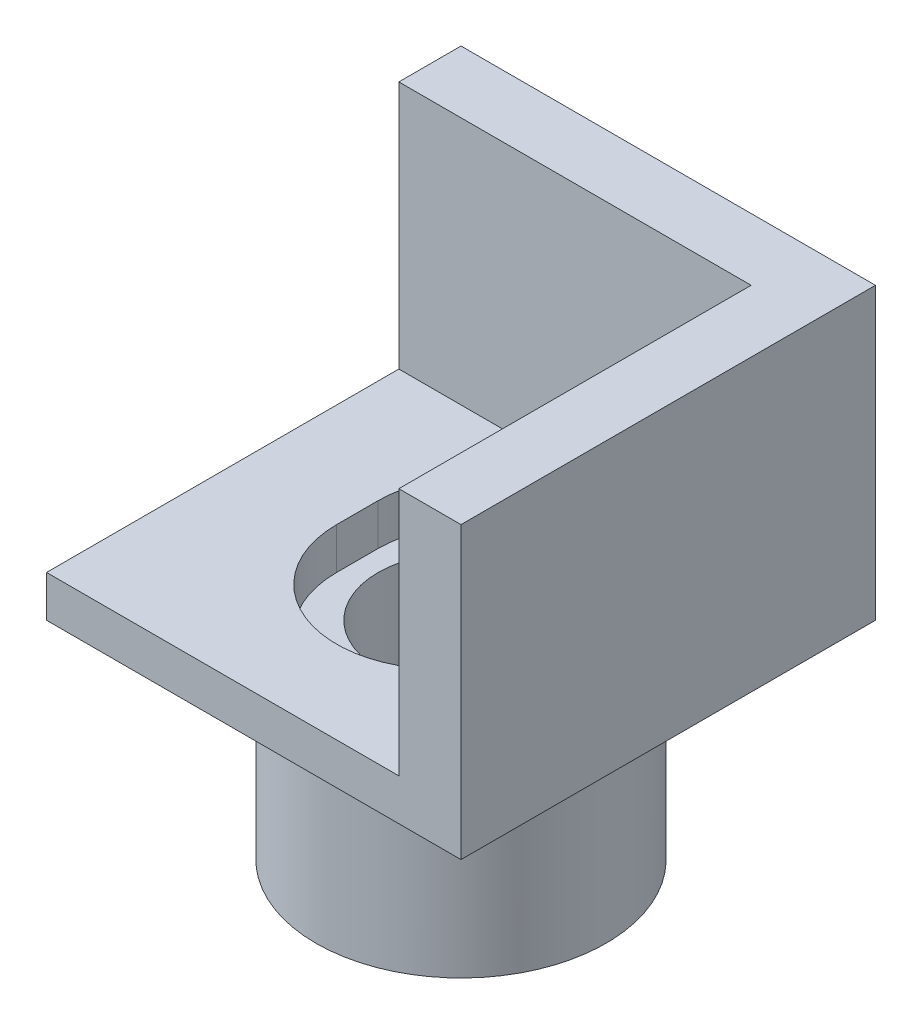
SolidWorks part; units mm, degrees
ref_plane "Front Plane" through (0, 0, 0) normal (0, 0, 1) x (1, 0, 0)
ref_plane "Top Plane" through (0, 0, 0) normal (0, 1, 0) x (1, 0, 0)
ref_plane "Right Plane" through (0, 0, 0) normal (1, 0, 0) x (0, 0, -1)
sketch "Sketch1" plane through (0, 0, 0) normal (0, 1, 0) x (1, 0, 0)
  line L0 (5, 5) -> (-5, -5) construction
  line L1 (-5, 5) -> (5, 5)
  line L2 (-5, 5) -> (-5, -5)
  line L3 (-5, -5) -> (5, -5)
  line L4 (5, 5) -> (5, -5)
  line L5 (5, -5) -> (-5, 5) construction
  point P0 (0, 0)
  dimension "D1" = 10
  dimension "D2" = 10
extrude "Boss-Extrude1" add sketch "Sketch1" along normal blind 1
sketch "Sketch2" plane through (0, 1, 0) normal (0, 1, 0) x (1, 0, 0)
  line L0 (0, 0.5) -> (0, -0.5) construction
  line L1 (2.5, 0.5) -> (2.5, -0.5)
  line L2 (-2.5, 0.5) -> (-2.5, -0.5)
  arc A0 (2.5, 0.5) -> (-2.5, 0.5) centre (0, 0.5) ccw
  arc A1 (-2.5, -0.5) -> (2.5, -0.5) centre (0, -0.5) ccw
  point P2 (0, 0)
  point P7 (0, 3)
  point P8 (0, -3)
  point P9 (0, 0)
  dimension "D1" = 5
  dimension "D2" = 6
extrude "Cut-Extrude1" cut sketch "Sketch2" against normal blind 1.5
sketch "Sketch3" plane through (0, 0, 0) normal (0, -1, 0) x (1, 0, 0)
  circle A3 centre (0, 0) radius 3.5
  dimension "D1" = 7
extrude "Boss-Extrude2" add sketch "Sketch3" along normal blind 5
sketch "Sketch4" plane through (0, 0, 0) normal (0, 1, 0) x (1, 0, 0)
  circle A0 centre (0, 0) radius 2
  dimension "D1" = 4
extrude "Cut-Extrude2" cut sketch "Sketch4" against normal through all
sketch "Sketch6" plane through (0, 1, 0) normal (0, 1, 0) x (1, 0, 0)
  line L3 (5, -5) -> (5, 5) construction
  line L4 (5, 5) -> (-5, 5) construction
  line L5 (3.5, -5) -> (3.5, 3.5)
  line L6 (3.5, 3.5) -> (-5, 3.5)
  line L7 (3.5, -5) -> (3.5, 3.5)
  line L8 (3.5, 3.5) -> (-5, 3.5)
  line L9 (5, -5) -> (5, 5)
  line L10 (5, 5) -> (-5, 5)
  line L11 (-5, 3.5) -> (-5, 5)
  line L12 (5, -5) -> (3.5, -5)
  dimension "D1" = 1.5
extrude "Boss-Extrude3" add sketch "Sketch6" along normal blind 6
